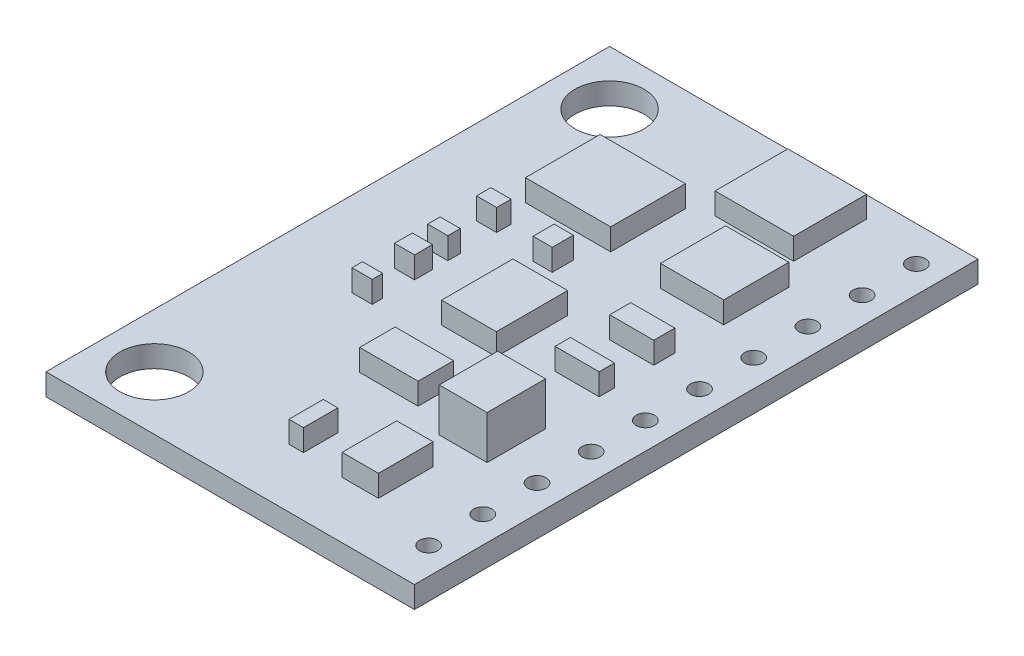
SolidWorks part; units mm, degrees
ref_plane "Front Plane" through (0, 0, 0) normal (0, 0, 1) x (1, 0, 0)
ref_plane "Top Plane" through (0, 0, 0) normal (0, 1, 0) x (1, 0, 0)
ref_plane "Right Plane" through (0, 0, 0) normal (1, 0, 0) x (0, 0, -1)
sketch "Sketch2" plane through (0, 0, 0) normal (0, 1, 0) x (1, 0, 0)
  line L1 (8.5, -13) -> (-8.5, -13)
  line L2 (8.5, -13) -> (8.5, 13)
  line L3 (8.5, 13) -> (-8.5, 13)
  line L4 (-8.5, -13) -> (-8.5, 13)
  line L5 (8.5, -13) -> (-8.5, 13) construction
  line L6 (8.5, 13) -> (-8.5, -13) construction
  point P0 (0, 0)
  dimension "D1" = 26
  dimension "D2" = 17
extrude "Boss-Extrude1" add sketch "Sketch2" along normal blind 1
sketch "Sketch3" plane through (0, 1, 0) normal (0, 1, 0) x (1, 0, 0)
  line L1 (-8.5, -13) -> (8.5, -13) construction
  line L2 (-8.5, 13) -> (-8.5, -13) construction
  line L3 (8.5, 13) -> (-8.5, 13) construction
  line L5 (8, -12.5) -> (-8, 12.5) construction
  line L6 (8, 12.5) -> (-8, -12.5) construction
  line L9 (0.7072, 12.0216) -> (4.3312, 12.0216)
  line L10 (0.7072, 12.0216) -> (0.7072, 8.6626)
  line L11 (0.7072, 8.6626) -> (4.3312, 8.6626)
  line L12 (4.3312, 12.0216) -> (4.3312, 8.6626)
  line L13 (2.3423, 7.5135) -> (5.2593, 7.5135)
  line L14 (2.3423, 7.5135) -> (2.3423, 4.5081)
  line L15 (2.3423, 4.5081) -> (5.2593, 4.5081)
  line L16 (5.2593, 7.5135) -> (5.2593, 4.5081)
  line L17 (-4.1988, 8.2648) -> (-0.2653, 8.2648)
  line L18 (-4.1988, 8.2648) -> (-4.1988, 4.8175)
  line L19 (-4.1988, 4.8175) -> (-0.2653, 4.8175)
  line L20 (-0.2653, 8.2648) -> (-0.2653, 4.8175)
  line L21 (-4.5966, 3.6241) -> (-3.6685, 3.6241)
  line L22 (-4.5966, 3.6241) -> (-4.5966, 2.9612)
  line L23 (-4.5966, 2.9612) -> (-3.6685, 2.9612)
  line L24 (-3.6685, 3.6241) -> (-3.6685, 2.9612)
  line L25 (-1.6796, 3.6241) -> (-0.7957, 3.6241)
  line L26 (-1.6796, 3.6241) -> (-1.6796, 2.6518)
  line L27 (-1.6796, 2.6518) -> (-0.7957, 2.6518)
  line L28 (-0.7957, 3.6241) -> (-0.7957, 2.6518)
  line L29 (-1.2376, 1.2817) -> (1.2864, 1.2817)
  line L30 (-1.2376, 1.2817) -> (-1.2376, -2.0101)
  line L31 (-1.2376, -2.0101) -> (1.2864, -2.0101)
  line L32 (1.2864, 1.2817) -> (1.2864, -2.0101)
  line L33 (-4.5966, 1.2817) -> (-3.6685, 1.2817)
  line L34 (-4.5966, 1.2817) -> (-4.5966, 0.7072)
  line L35 (-4.5966, 0.7072) -> (-3.6685, 0.7072)
  line L36 (-3.6685, 1.2817) -> (-3.6685, 0.7072)
  line L37 (-4.5966, 0) -> (-3.6685, 0)
  line L38 (-4.5966, 0) -> (-4.5966, -0.8252)
  line L39 (-4.5966, -0.8252) -> (-3.6685, -0.8252)
  line L40 (-3.6685, 0) -> (-3.6685, -0.8252)
  line L41 (-4.5966, -2.2982) -> (-3.6685, -2.2982)
  line L42 (-4.5966, -2.2982) -> (-4.5966, -2.7844)
  line L43 (-4.5966, -2.7844) -> (-3.6685, -2.7844)
  line L44 (-3.6685, -2.2982) -> (-3.6685, -2.7844)
  line L45 (-1.2376, -4.1545) -> (1.4584, -4.1545)
  line L46 (-1.2376, -4.1545) -> (-1.2376, -5.7898)
  line L47 (-1.2376, -5.7898) -> (1.4584, -5.7898)
  line L48 (1.4584, -4.1545) -> (1.4584, -5.7898)
  line L49 (3.2263, 2.254) -> (5.2593, 2.254)
  line L50 (3.2263, 2.254) -> (3.2263, 1.2817)
  line L51 (3.2263, 1.2817) -> (5.2593, 1.2817)
  line L52 (5.2593, 2.254) -> (5.2593, 1.2817)
  line L53 (3.2263, -0.5304) -> (5.2593, -0.5304)
  line L54 (3.2263, -0.5304) -> (3.2263, -1.2375)
  line L55 (3.2263, -1.2375) -> (5.2593, -1.2375)
  line L56 (5.2593, -0.5304) -> (5.2593, -1.2375)
  line L57 (2.5488, -7.8671) -> (4.2249, -7.8671)
  line L58 (2.5488, -7.8671) -> (2.5488, -10.3863)
  line L59 (2.5488, -10.3863) -> (4.2249, -10.3863)
  line L60 (4.2249, -7.8671) -> (4.2249, -10.3863)
  line L61 (0, -8.7068) -> (0.6703, -8.7068)
  line L62 (0, -8.7068) -> (0, -10.2907)
  line L63 (0, -10.2907) -> (0.6703, -10.2907)
  line L64 (0.6703, -8.7068) -> (0.6703, -10.2907)
  circle A0 centre (-6, -10.5) radius 0.8256
  circle A1 centre (-6, 10.5) radius 0.7991
  circle A3 centre (7.2667, 11.3855) radius 0.0168
  circle A4 centre (7.2667, 11.3855) radius 0.4
  point P0 (0, 0)
  dimension "D1" = 0.8
  dimension "D2" = 2.5
  dimension "D3" = 2.5
  dimension "D4" = 2.5
  dimension "D5" = 2.5
extrude "Boss-Extrude2" add sketch "Sketch3" along normal blind 1
sketch "Sketch4" plane through (0, 2, 0) normal (0, 1, 0) x (1, 0, 0)
  circle A0 centre (-6, 10.5) radius 1.59
  circle A1 centre (-6, -10.5) radius 1.59
  circle A2 centre (7.2667, 11.3855) radius 0.42
  circle A3 centre (7.2667, 8.8855) radius 0.42
  circle A4 centre (7.2667, 6.3855) radius 0.42
  circle A5 centre (7.2667, 3.8855) radius 0.42
  circle A6 centre (7.2667, 1.3855) radius 0.42
  circle A7 centre (7.2667, -1.1145) radius 0.42
  circle A8 centre (7.2667, -3.6145) radius 0.42
  circle A9 centre (7.2667, -6.1145) radius 0.42
  circle A10 centre (7.2667, -8.6145) radius 0.42
  circle A11 centre (7.2667, -11.1145) radius 0.42
  dimension "D2" = 0.84
  dimension "D3" = 3.18
  dimension "D4" = 3.18
  dimension "D1" = 10
extrude "Cut-Extrude1" cut sketch "Sketch4" against normal through all
sketch "Sketch5" plane through (0, 1, 0) normal (0, 1, 0) x (1, 0, 0)
  line L1 (3.0938, -3.7567) -> (5.3036, -3.7567)
  line L2 (3.0938, -3.7567) -> (3.0938, -6.4528)
  line L3 (3.0938, -6.4528) -> (5.3036, -6.4528)
  line L4 (5.3036, -3.7567) -> (5.3036, -6.4528)
extrude "Boss-Extrude3" add sketch "Sketch5" along normal blind 2
